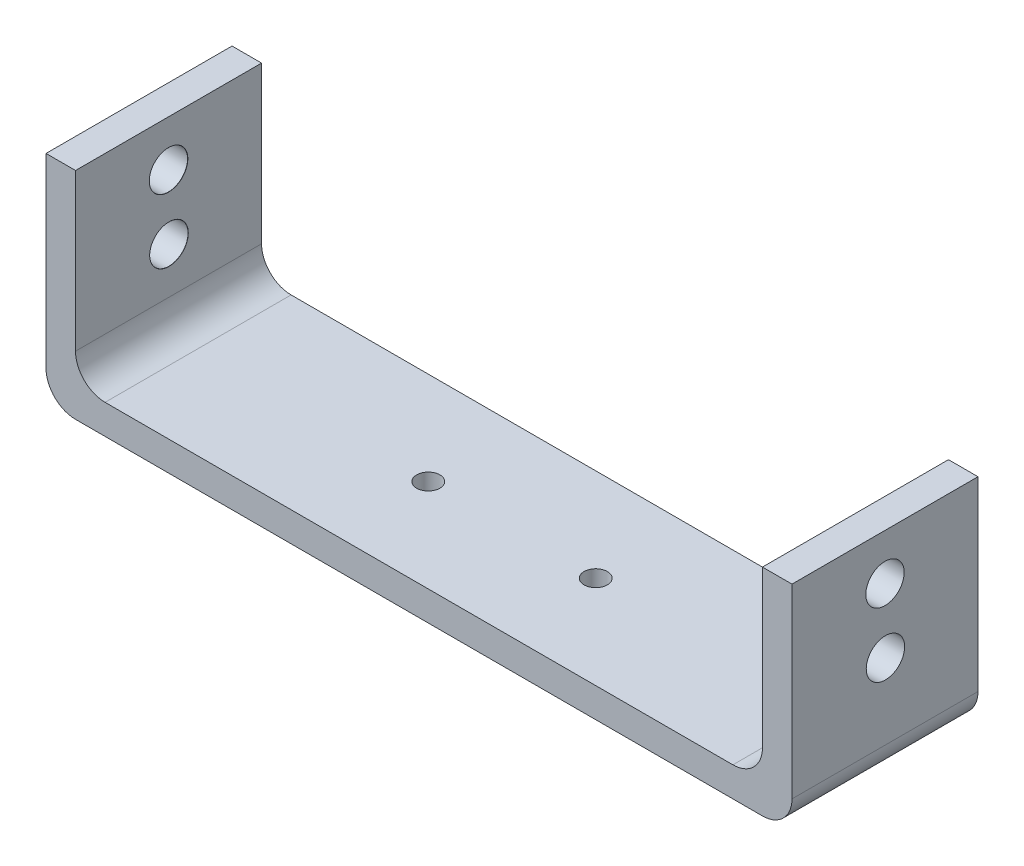
SolidWorks part; units mm, degrees
ref_plane "Front Plane" through (0, 0, 0) normal (0, 0, 1) x (1, 0, 0)
ref_plane "Top Plane" through (0, 0, 0) normal (0, 1, 0) x (1, 0, 0)
ref_plane "Right Plane" through (0, 0, 0) normal (1, 0, 0) x (0, 0, -1)
sketch "Sketch1" plane through (0, 0, 0) normal (0, 1, 0) x (1, 0, 0)
  line L1 (-154.05, 40) -> (0, 40)
  line L2 (-154.05, 40) -> (-154.05, 0)
  line L3 (-154.05, 0) -> (0, 0)
  line L4 (0, 40) -> (0, 0)
  dimension "D1" = 40
  dimension "D2" = 154.05
  dimension "D3" = 0
  dimension "D4" = 0
extrude "Boss-Extrude1" add sketch "Sketch1" along normal blind 6.35
sketch "Sketch2" plane through (0, 6.35, 0) normal (0, 1, 0) x (1, 0, 0)
  line L0 (0, 40) -> (-154.05, 40) construction
  line L1 (-6.35, 40) -> (0, 40)
  line L2 (-6.35, 40) -> (-6.35, 0)
  line L3 (-6.35, 0) -> (0, 0)
  line L4 (0, 40) -> (0, 0)
  line L5 (0, 0) -> (0, 40) construction
  line L6 (-154.05, 0) -> (0, 0) construction
  dimension "D1" = 0
  dimension "D2" = 0
  dimension "D3" = 0
  dimension "D4" = 6.35
extrude "Boss-Extrude2" add sketch "Sketch2" along normal blind 40
fillet "Fillet1" radius 6.35 2 edges at (0, 0, -20) (-6.35, 6.35, -20)
hole_wizard "Tap Drill for M8 Helicoil1" positions "Sketch4" profile "Sketch5" hole size "M8x1.0" standard "ANSI Metric"
sketch "Sketch4" plane through (-6.35, 0, 0) normal (-1, 0, 0) x (0, 0, 1)
  line L0 (0, 46.35) -> (0, 12.7) construction
  line L1 (-40, 46.35) -> (0, 46.35) construction
  line L2 (-40, 12.7) -> (0, 12.7) construction
  point P0 (-20, 36.467)
  point P2 (-20.0935, 22.583)
  dimension "D1" = 20
  dimension "D2" = 9.883
  dimension "D3" = 9.883
sketch "Sketch5" plane through (-6.35, 36.467, -20) normal (0, 1, 0) x (0, 0, 1)
  line L0 (0, 0) -> (0, 6.35)
  line L1 (0, 6.35) -> (4.125, 6.35)
  line L2 (4.125, 6.35) -> (4.125, 0.025)
  line L3 (4.125, 0.025) -> (4.15, 0)
  line L5 (4.15, 0) -> (0, 0)
  line L6 (-4.125, 0.025) -> (-4.15, 0) construction
  line L11 (0, -6.35) -> (0, 107.95) construction
  dimension "Thru Hole Dia." = 8.25
  dimension "Thru Hole Depth" = 6.35
  dimension "Near C'Sink Dia." = 8.3
  dimension "Near C'Sink Angle" = 90
ref_plane "Plane1" through (-80.2, 0, 0) normal (-1, 0, 0) x (0, 0, 1)
mirror "Mirror1" about plane through (-80.2, 0, 0) normal (-1, 0, 0) of "Boss-Extrude1", "Tap Drill for M8 Helicoil1", "Boss-Extrude2", "Fillet1"
sketch "Sketch6" plane through (0, 6.35, 0) normal (0, 1, 0) x (1, 0, 0)
  line L0 (-12.7, 40) -> (-147.7, 40) construction
  line L1 (-12.7, 0) -> (-12.7, 40) construction
  circle A0 centre (-98.2, 20) radius 2.5
  circle A1 centre (-62.2, 20) radius 2.5
  dimension "D3" = 5
  dimension "D4" = 5
  dimension "D6" = 49.5
  dimension "D1" = 20
  dimension "D2" = 20
  dimension "D5" = 36
extrude "Cut-Extrude1" cut sketch "Sketch6" against normal blind 40
